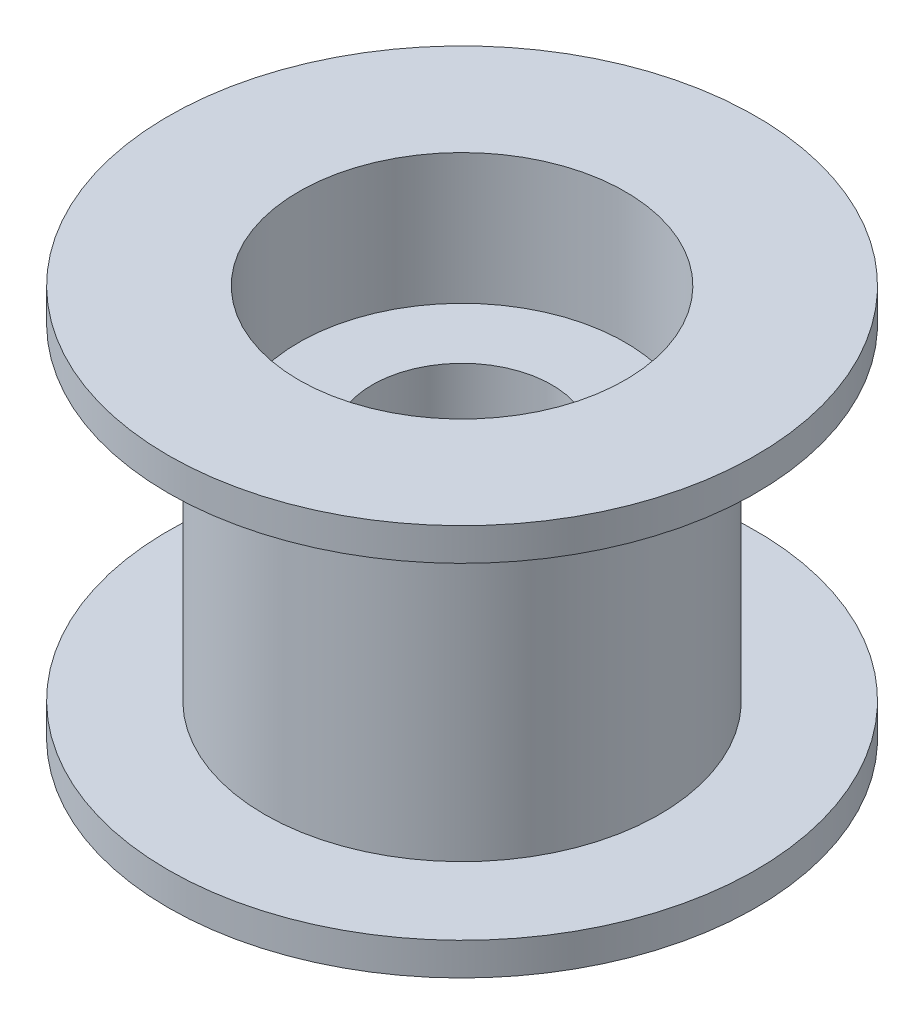
SolidWorks part; units mm, degrees
material "6061-T6 (SS)"
ref_plane "Front" through (0, 0, 0) normal (0, 0, 1) x (1, 0, 0)
ref_plane "Top" through (0, 0, 0) normal (0, 1, 0) x (1, 0, 0)
ref_plane "Right" through (0, 0, 0) normal (1, 0, 0) x (0, 0, -1)
sketch "Sketch1" plane through (0, 0, 0) normal (0, 0, 1) x (1, 0, 0)
  line L0 (0, 6) -> (0, -6) construction
  line L1 (0, -6) -> (-5, -6) construction
  line L2 (-5, -6) -> (-5, 6) construction
  line L3 (-5, 6) -> (0, 6) construction
  line L4 (-5, 6) -> (-9, 6)
  line L5 (-9, 6) -> (-9, 5)
  line L6 (-9, 5) -> (-6.05, 5)
  line L7 (-6.05, 5) -> (-6.05, -5)
  line L8 (-6.05, 0) -> (0, 0) construction
  line L9 (-5, 6) -> (-5, 2)
  line L10 (-5, 2) -> (-2.75, 2)
  line L11 (-2.75, 2) -> (-2.75, -2)
  line L12 (-5, -2) -> (-2.75, -2)
  line L13 (-5, -6) -> (-5, -2)
  line L14 (-5, -6) -> (-9, -6)
  line L15 (-9, -6) -> (-9, -5)
  line L16 (-9, -5) -> (-6.05, -5)
  point P4 (0, 0)
  point P16 (-2.75, 0)
  dimension "D1" = 12
  dimension "D2" = 5.5
  dimension "D3" = 10
  dimension "D4" = 18
  dimension "D5" = 12.1
  dimension "D6" = 4
  dimension "D7" = 10
revolve "Revolve1" add sketch "Sketch1" angle 360 about L0
